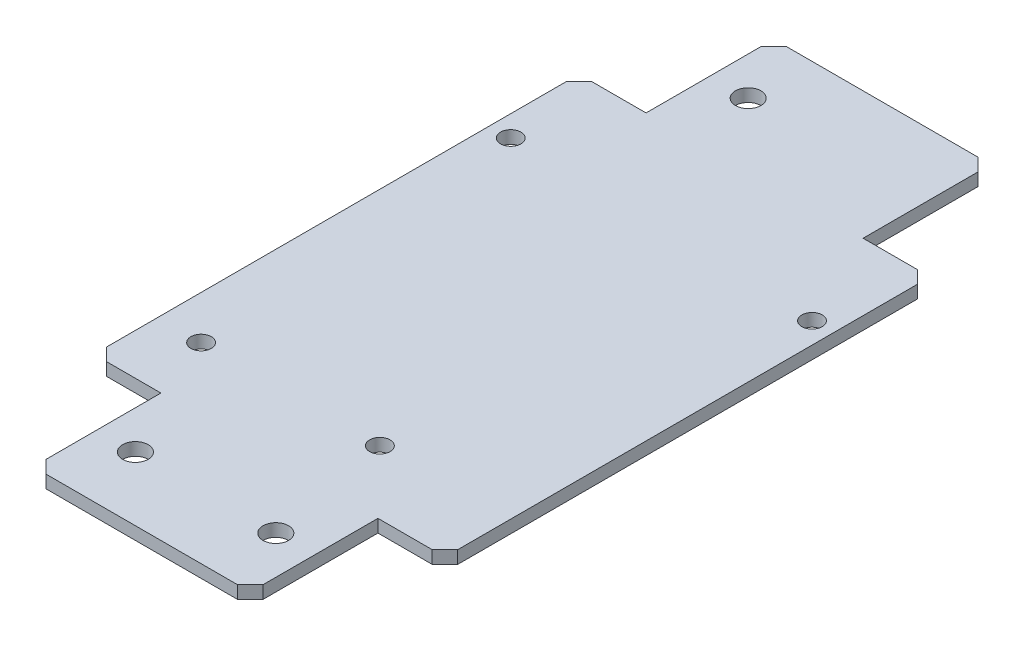
SolidWorks part; units mm, degrees
ref_plane "Ön Düzlem" through (0, 0, 0) normal (0, 0, 1) x (1, 0, 0)
ref_plane "Üst Düzlem" through (0, 0, 0) normal (0, 1, 0) x (1, 0, 0)
ref_plane "Sağ Düzlem" through (0, 0, 0) normal (1, 0, 0) x (0, 0, -1)
sketch "Sketch1" plane through (0, 50.6628, 0) normal (0, 1, 0) x (1, 0, 0)
  line L0 (-85.7032, -20) -> (-85.7032, -40)
  line L1 (-210.5846, -20) -> (69.4154, -20) construction
  line L2 (-210.5846, -40) -> (69.4154, -40) construction
  line L3 (-85.7032, -40) -> (-96.2032, -40)
  line L4 (-96.2032, -40) -> (-96.2032, -116)
  line L5 (-210.5846, -116) -> (69.4154, -116) construction
  line L6 (-96.2032, -116) -> (-85.7032, -116)
  line L7 (-85.7032, -116) -> (-85.7032, -136)
  line L8 (-210.5846, -136) -> (69.4154, -136) construction
  line L9 (-85.7032, -136) -> (-51.7032, -136)
  line L10 (-51.7032, -136) -> (-51.7032, -116)
  line L11 (-51.7032, -116) -> (-41.2032, -116)
  line L12 (-41.2032, -116) -> (-41.2032, -40)
  line L13 (-41.2032, -40) -> (-51.7032, -40)
  line L14 (-51.7032, -40) -> (-51.7032, -20)
  line L15 (-51.7032, -20) -> (-85.7032, -20)
  circle A0 centre (-79.7032, -30) radius 2
  circle A1 centre (-79.7032, -126) radius 2
  circle A2 centre (-57.7032, -126) radius 2
  dimension "D4" = 4
  dimension "D1" = 55
  dimension "D2" = 34
  dimension "D3" = 10.5
  dimension "D5" = 10
  dimension "D6" = 6
  dimension "D7" = 10
  dimension "D8" = 6
  dimension "D9" = 6
extrude "Boss-Extrude1" add sketch "Sketch1" along normal blind 2
sketch "Sketch2" plane through (0, 52.6628, 0) normal (0, 1, 0) x (1, 0, 0)
  circle A0 centre (-92.9032, -54) radius 1.6
  circle A1 centre (-44.5032, -55.2) radius 1.6
  circle A2 centre (-89.4032, -106) radius 1.6
  circle A3 centre (-61.4032, -106) radius 1.6
  dimension "D1" = 3.2
extrude "Cut-Extrude1" cut sketch "Sketch2" against normal blind 10
chamfer "Chamfer1" distance 2 angle 45 8 edges at (-41.2032, 51.6628, 40) (-41.2032, 51.6628, 116) (-51.7032, 51.6628, 136) (-85.7032, 51.6628, 136) (-96.2032, 51.6628, 116) (-96.2032, 51.6628, 40) (-85.7032, 51.6628, 20) (-51.7032, 51.6628, 20)
